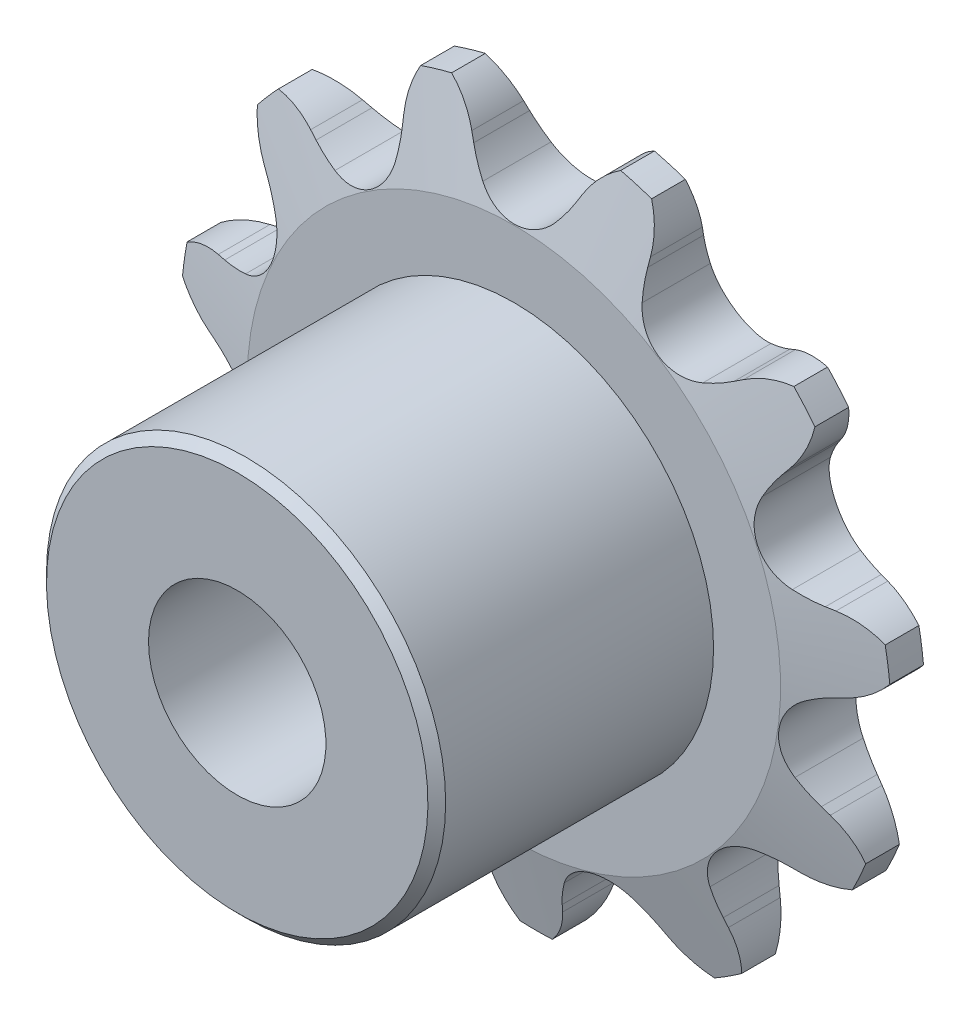
SolidWorks part; units mm, degrees
ref_plane "Front Plane" through (0, 0, 0) normal (0, 0, 1) x (1, 0, 0)
ref_plane "Top Plane" through (0, 0, 0) normal (0, 1, 0) x (1, 0, 0)
ref_plane "Right Plane" through (0, 0, 0) normal (1, 0, 0) x (0, 0, -1)
sketch "Sketch0" plane through (0, 0, 0) normal (0, 0, 1) x (1, 0, 0)
  line L0 (3.175, -10.8131) -> (0, 0) construction
  line L1 (0, 0) -> (8.517, -7.38) construction
  line L2 (0, 0) -> (-3.175, -10.8131) construction
  line L3 (3.175, -10.8131) -> (8.517, -7.38) construction
  line L4 (3.175, -10.8131) -> (-3.175, -10.8131) construction
  line L5 (5.0677, -10.2355) -> (4.8552, -10.0148)
  line L6 (3.175, -10.8131) -> (0, -11.7453) construction
  line L7 (1.2705, -11.3504) -> (1.3299, -11.0499)
  line L8 (0, -10.8131) -> (0, -12.7181) construction
  line L9 (4.104, -9.3925) -> (1.7293, -13.0239) construction
  line L10 (0, 0) -> (0, -10.8131) construction
  line L11 (4.8552, -10.0148) -> (1.7293, -13.0239) construction
  line L12 (0, -12.7181) -> (0, -13.1757) construction
  line L13 (7.0639, -8.3138) -> (5.0677, -10.2355) construction
  circle A0 centre (0, 0) radius 12.7181 construction
  circle A1 centre (0, 0) radius 11.2696 construction
  arc A2 (-1.8155, -13.5595) -> (8.8581, -10.4254) centre (0, 0) ccw
  circle A3 centre (0, 0) radius 13.1757 construction
  circle A4 centre (3.175, -10.8131) radius 1.651 construction
  arc A7 (4.104, -9.3925) -> (1.6255, -10.1202) centre (3.175, -10.8131) ccw
  circle A8 centre (3.175, -10.8131) radius 1.6974 construction
  arc A9 (5.0677, -10.2355) -> (8.8581, -10.4254) centre (7.0639, -8.3138) ccw
  arc A10 (4.8552, -10.0148) -> (4.104, -9.3925) centre (1.7293, -13.0239) ccw
  arc A11 (1.2705, -11.3504) -> (-1.8155, -13.5595) centre (-1.4478, -10.8131) cw
  arc A12 (1.3299, -11.0499) -> (1.6255, -10.1202) centre (5.5865, -11.8913) cw
  dimension "D1" = 1.6974
  dimension "R" = 1.6974
sketch "Sketch1" plane through (0, 0, 0) normal (1, 0, 0) x (0, 0, -1)
  line L0 (1.397, 0) -> (-1.397, 0)
  line L1 (-1.397, 0) -> (-1.397, 9.5431)
  line L2 (-1.397, 9.5431) -> (-0.6033, 12.7181)
  line L3 (-0.6033, 12.7181) -> (0.6033, 12.7181)
  line L4 (0.6033, 12.7181) -> (1.397, 9.5431)
  line L5 (1.397, 9.5431) -> (1.397, 0)
  line L7 (0, 12.7181) -> (0, 0) construction
  line L8 (-1.397, 9.5431) -> (1.397, 9.5431) construction
  line L9 (0, 12.7181) -> (0, -12.7181) construction
  line L10 (-1.397, 9.5431) -> (-1.397, 12.7181) construction
  line L11 (-1.397, 12.7181) -> (-0.6033, 12.7181) construction
  line L12 (0.6033, 12.7181) -> (1.397, 12.7181) construction
  line L13 (1.397, 12.7181) -> (1.397, 9.5431) construction
  line L14 (0, 0) -> (-6.4008, 0) construction
  line L22 (1.397, 0) -> (-11.303, 0) construction
  line L24 (-1.397, 0) -> (-1.397, 7.2571) construction
revolve "Revolve1" add sketch "Sketch1" angle 360 mid plane about L0
extrude "Cut-Extrude1" cut sketch "Sketch0" against normal through all and the other way through all
pattern_circular "CirPattern1" count 11 over 360 about axis through (0, 0, 0) along (0, 0, 1) of "Cut-Extrude1"
sketch "Sketch2" plane through (0, 0, 0) normal (0, 0, 1) x (1, 0, 0)
  circle A0 centre (0, 0) radius 3.175 construction
  circle A1 centre (0, 0) radius 7.1438
  circle A2 centre (0, 0) radius 12.7 construction
  dimension "Bore" = 6.35
  dimension "Hub Dia." = 14.2875
  dimension "OD" = 25.4
extrude "Boss-Extrude1" add sketch "Sketch2" along normal up to vertex (11.303 mm away) from surface at 1.397 starting at face at (-9.5431, 0, 1.397)
sketch "Sketch3" plane through (0, 0, 0) normal (0, 0, 1) x (1, 0, 0)
  circle A0 centre (0, 0) radius 3.175 construction
  circle A1 centre (0, 0) radius 3.175
extrude "Cut-Extrude2" cut sketch "Sketch3" along normal through all and the other way through all
sketch "Sketch4" plane through (0, 0, 0) normal (1, 0, 0) x (0, 0, -1)
  line L0 (-11.303, 7.1438) -> (-11.303, 6.8263)
  line L1 (-1.397, 12.7181) -> (-3.4925, 12.7181)
  line L2 (-1.397, 12.7181) -> (-1.397, 7.2571)
  line L3 (-1.397, 7.2571) -> (-3.4925, 7.2571)
  line L4 (-3.4925, 12.7181) -> (-3.4925, 7.2571)
  line L9 (-11.303, 6.8263) -> (-10.9855, 7.1438)
  line L10 (-10.9855, 7.1438) -> (-11.303, 7.1438)
  dimension "C" = 0.3175
  dimension "D3" = 2.0955
revolve "Cut-Revolve1" cut sketch "Sketch4" angle 360 mid plane about L22
equation "\"360/N@Sketch0\" = 360/\"Teeth@CirPattern1\""
equation "\"Ds@Sketch0\" = 1.005 * \"Dr@Sketch0\" + 0.003"
equation "\"R@Sketch0\" = 1/2 * \"Ds@Sketch0\""
equation "\"A@Sketch0\" = 35 +  ( 60 / \"Teeth@CirPattern1\" ) "
equation "\"B@Sketch0\" = 18 -  ( 56 / \"Teeth@CirPattern1\" )"
equation "\"ac@Sketch0\" = 0.8 * \"Dr@Sketch0\""
equation "\"ab@Sketch0\" = 1.4 * \"Dr@Sketch0\""
equation "\"J@Sketch0\" = 0.3 * \"Pitch@Sketch0\""
equation "\"h@Sketch1\" = \"Pitch@Sketch0\" / 2"
equation "\"g@Sketch1\" = \"h@Sketch1\" / 4"
equation "\"MHD@Sketch1\" = \"Pitch@Sketch0\" * ( cotan ( 180 / \"Teeth@CirPattern1\" ) - 1 ) - 0.030"
equation "\"D3@Sketch4\" = \"t@Sketch1\" * 3 / 4"
